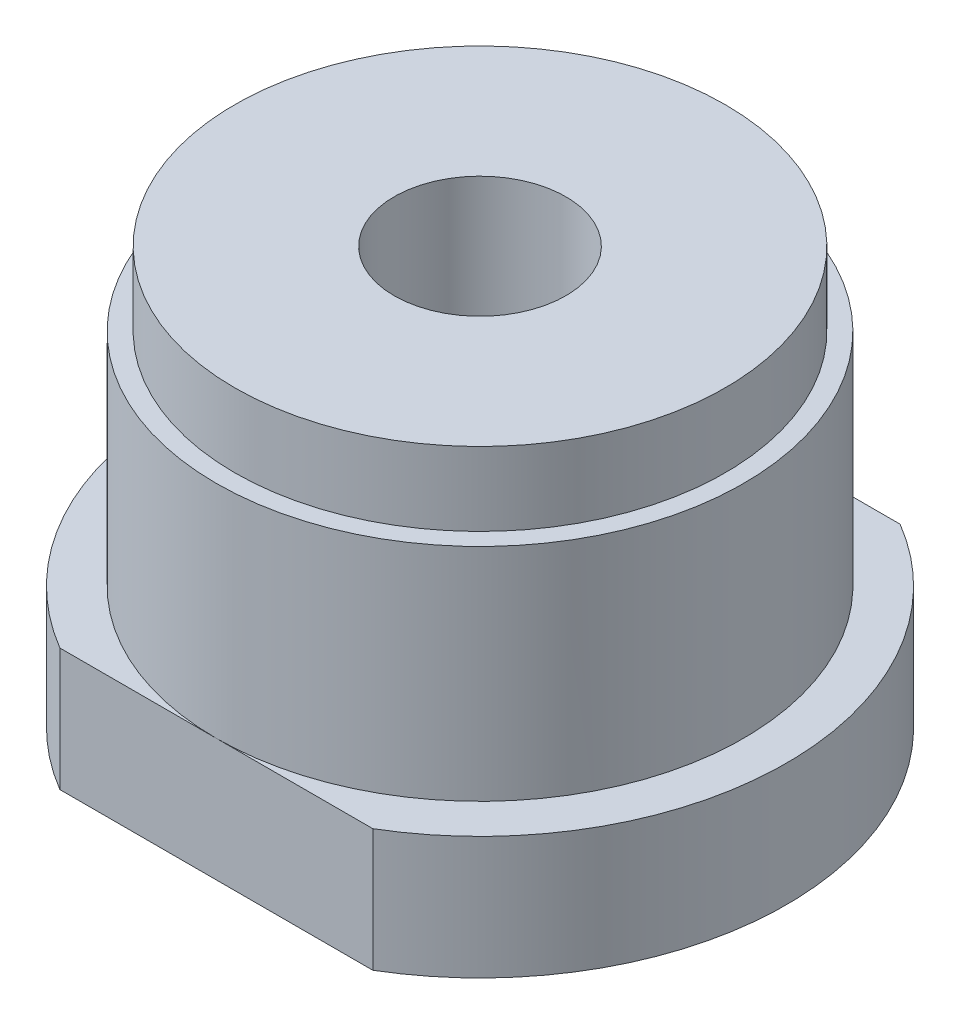
SolidWorks part; units mm, degrees
ref_plane "Front Plane" through (0, 0, 0) normal (0, 0, 1) x (1, 0, 0)
ref_plane "Top Plane" through (0, 0, 0) normal (0, 1, 0) x (1, 0, 0)
ref_plane "Right Plane" through (0, 0, 0) normal (1, 0, 0) x (0, 0, -1)
sketch "Sketch1" plane through (0, 0, 0) normal (0, 1, 0) x (1, 0, 0)
  circle A0 centre (0, 0) radius 12.5
  dimension "D1" = 25
extrude "Boss-Extrude1" add sketch "Sketch1" along normal blind 17
sketch "Sketch2" plane through (0, 17, 0) normal (0, 1, 0) x (1, 0, 0)
  circle A0 centre (0, 0) radius 3.5
  dimension "D1" = 7
extrude "Cut-Extrude1" cut sketch "Sketch2" against normal offset from surface (15 mm away) 2 up to face at (0, 0, 12.5)
sketch "Sketch3" plane through (0, 0, 0) normal (1, 0, 0) x (0, 0, -1)
  line L0 (0, 11) -> (0, -11) construction
  line L1 (13.75, 0) -> (-13.75, 0) construction
  circle A0 centre (8, 3) radius 1.5
  dimension "D1" = 3
  dimension "D2" = 8
  dimension "D3" = 3
extrude "Cut-Extrude2" [suppressed] cut sketch "Sketch3" against normal through all and the other way through all
mirror "Mirror1" [suppressed] about plane through (0, 0, 0) normal (0, 0, 1)
sketch "Sketch4" plane through (0, 17, 0) normal (0, 1, 0) x (1, 0, 0)
  circle A0 centre (0, 0) radius 10
  dimension "D1" = 20
extrude "Cut-Extrude3" cut sketch "Sketch4" against normal offset from surface (12 mm away) 5 flip side to cut up to face at (0, 0, 12.5)
sketch "Sketch5" plane through (0, 0, 0) normal (0, -1, 0) x (1, 0, 0)
  line L0 (9.35, 0) -> (-9.35, 0) construction
  circle A0 centre (-8, 0) radius 1.25
  dimension "D1" = 2.5
  dimension "D2" = 8
extrude "Cut-Extrude4" cut sketch "Sketch5" against normal blind 10
mirror "Mirror2" about plane through (0, 0, 0) normal (1, 0, 0) of "Cut-Extrude4"
sketch "Sketch6" plane through (0, 5, 0) normal (0, 1, 0) x (1, 0, 0)
  line L0 (0, -9.35) -> (0, 9.35) construction
  circle A0 centre (0, 12.5) radius 2.5
  circle A1 centre (0, 0) radius 10 construction
  dimension "D1" = 5
extrude "Cut-Extrude5" [suppressed] cut sketch "Sketch6" against normal blind 5
sketch "Sketch8" plane through (0, 5, 0) normal (0, 1, 0) x (1, 0, 0)
  circle A0 centre (0, 0) radius 10.75
  circle A1 centre (0, 0) radius 4
  dimension "D1" = 21.5
extrude "Boss-Extrude3" add sketch "Sketch8" along normal blind 9
sketch "Sketch7" plane through (0, 5, 0) normal (0, 1, 0) x (1, 0, 0)
  line L1 (-11.0868, 15.6344) -> (11.839, 15.6344)
  line L2 (-11.0868, 15.6344) -> (-11.0868, 10.75)
  line L3 (-11.0868, 10.75) -> (11.839, 10.75)
  line L4 (11.839, 15.6344) -> (11.839, 10.75)
  circle A0 centre (0, 0) radius 10.75 construction
extrude "Cut-Extrude6" cut sketch "Sketch7" against normal through all
mirror "Mirror3" about plane through (0, 0, 0) normal (0, 0, 1) of "Cut-Extrude6"
pattern_circular "CirPattern1" [suppressed] count 12 over 360
fillet "Fillet1" [suppressed] radius 1
